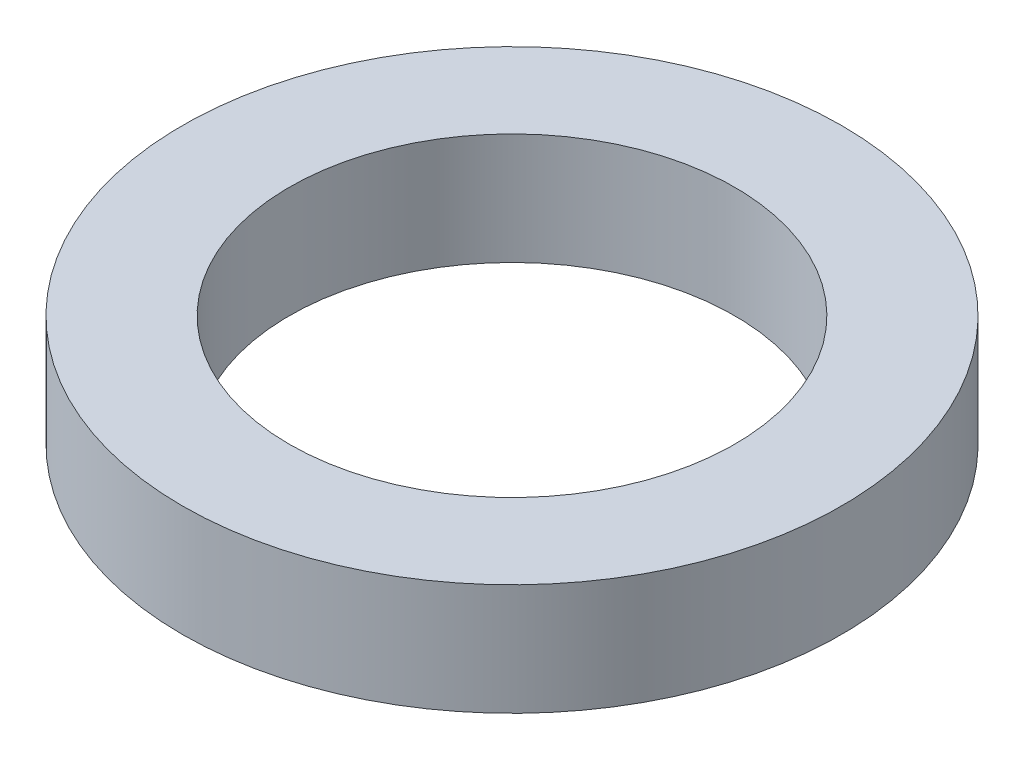
SolidWorks part; units mm, degrees
ref_plane "Front Plane" through (0, 0, 0) normal (0, 0, 1) x (1, 0, 0)
ref_plane "Top Plane" through (0, 0, 0) normal (0, 1, 0) x (1, 0, 0)
ref_plane "Right Plane" through (0, 0, 0) normal (1, 0, 0) x (0, 0, -1)
sketch "Sketch1" plane through (0, 0, 0) normal (0, 1, 0) x (1, 0, 0)
  circle A0 centre (0, 0) radius 3.175
  circle A1 centre (0, 0) radius 4.699
  dimension "D1" = 6.35
  dimension "D2" = 9.398
extrude "Boss-Extrude1" add sketch "Sketch1" along normal blind 1.5875
